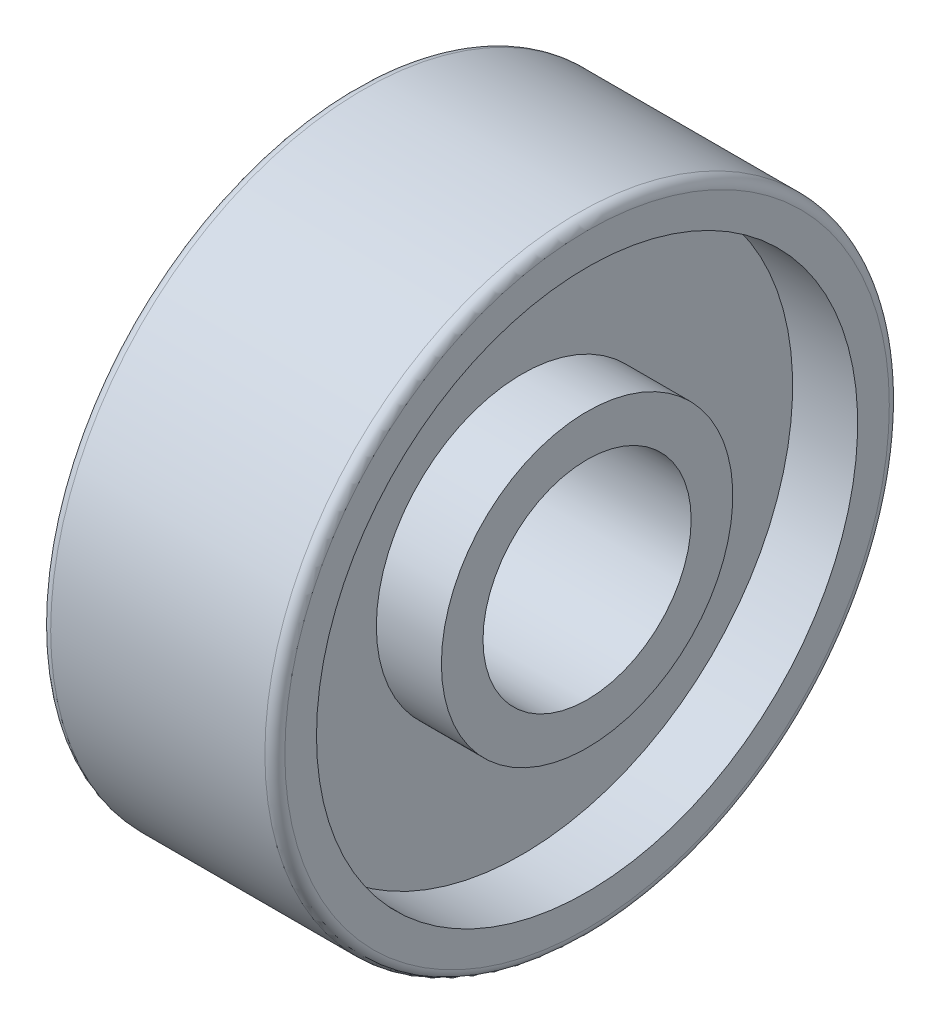
SolidWorks part; units mm, degrees
ref_plane "Front" through (0, 0, 0) normal (0, 0, 1) x (1, 0, 0)
ref_plane "Top" through (0, 0, 0) normal (0, 1, 0) x (1, 0, 0)
ref_plane "Right" through (0, 0, 0) normal (1, 0, 0) x (0, 0, -1)
sketch "Sketch3" plane through (0, 0, 0) normal (0, 0, 1) x (1, 0, 0)
  line L0 (-4.8321, 0) -> (5.0556, 0) construction
  line L1 (0.3048, 3.175) -> (7.1437, 3.175)
  line L2 (7.1437, 3.175) -> (7.1437, 4.445)
  line L3 (7.1437, 4.445) -> (5.1594, 4.445)
  line L4 (5.1594, 4.445) -> (5.1594, 8.255)
  line L5 (5.1594, 8.255) -> (7.1437, 8.255)
  line L6 (7.1437, 8.255) -> (7.1437, 9.2202)
  line L9 (6.8389, 9.525) -> (0.3048, 9.525)
  line L10 (0, 9.2202) -> (0, 8.255)
  line L11 (0, 8.255) -> (1.9844, 8.255)
  line L12 (1.9844, 8.255) -> (1.9844, 4.445)
  line L13 (1.9844, 4.445) -> (0, 4.445)
  line L14 (0, 4.445) -> (0, 3.4798)
  line L15 (0, 3.175) -> (0, 0) construction
  arc A0 (0, 3.4798) -> (0.3048, 3.175) centre (0.3048, 3.4798) ccw
  arc A1 (0.3048, 9.525) -> (0, 9.2202) centre (0.3048, 9.2202) ccw
  arc A2 (7.1437, 9.2202) -> (6.8389, 9.525) centre (6.8389, 9.2202) ccw
  point P23 (0, 9.525)
  dimension "R" = 0.3048
  dimension "ID" = 6.35
  dimension "OD" = 19.05
  dimension "W" = 7.1437
  dimension "BALLDIA" = 3.175
  dimension "IRT" = 1.27
  dimension "ORT" = 1.27
revolve "bearing-revolution" add sketch "Sketch3" angle 360 about L0
